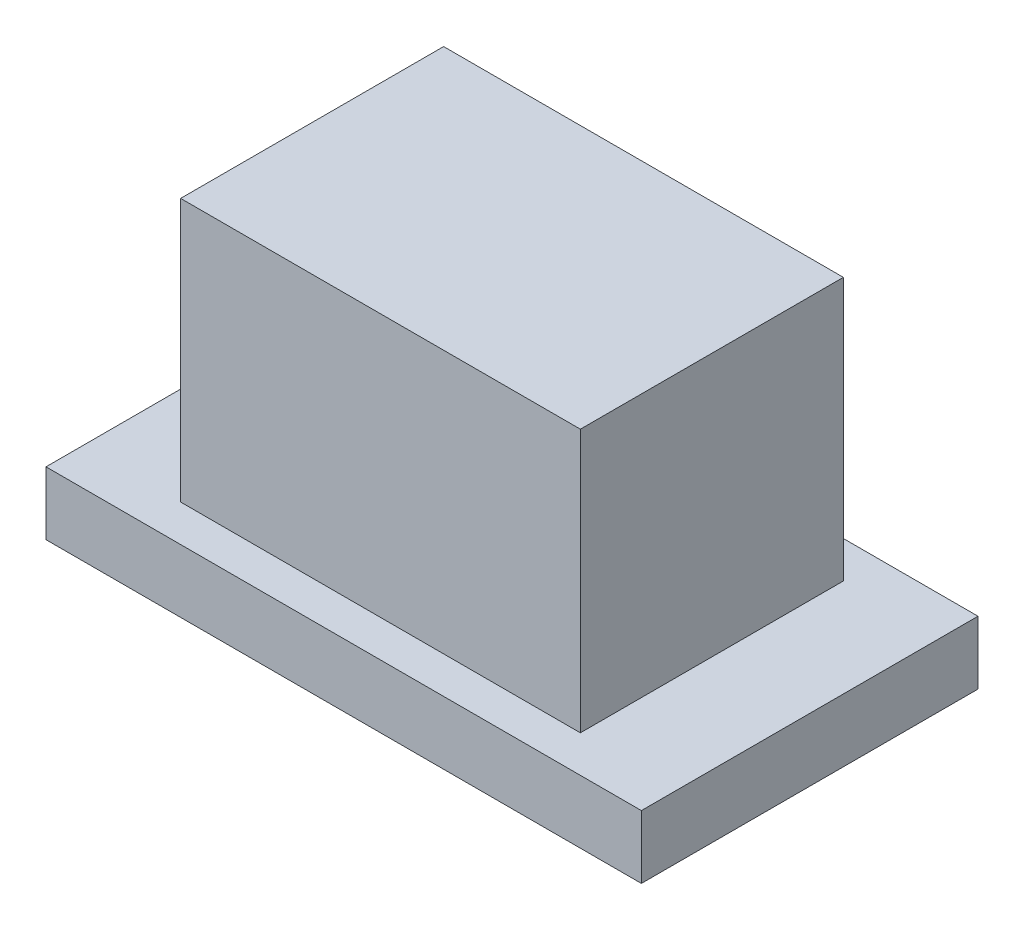
SolidWorks part; units mm, degrees
ref_plane "Front Plane" through (0, 0, 0) normal (0, 0, 1) x (1, 0, 0)
ref_plane "Top Plane" through (0, 0, 0) normal (0, 1, 0) x (1, 0, 0)
ref_plane "Right Plane" through (0, 0, 0) normal (1, 0, 0) x (0, 0, -1)
sketch "Sketch1" plane through (0, 0, 0) normal (0, 1, 0) x (1, 0, 0)
  line L1 (-8.6633, 6.0372) -> (19.6367, 6.0372)
  line L2 (-8.6633, 6.0372) -> (-8.6633, -9.9628)
  line L3 (-8.6633, -9.9628) -> (19.6367, -9.9628)
  line L4 (19.6367, 6.0372) -> (19.6367, -9.9628)
  point P4 (19.6367, -1.9628)
  dimension "D1" = 28.3
  dimension "D2" = 16
extrude "Boss-Extrude1" add sketch "Sketch1" along normal blind 3
sketch "Sketch2" plane through (0, 3, 0) normal (0, 1, 0) x (1, 0, 0)
  line L0 (5.4867, 6.0372) -> (5.4867, -9.9628) construction
  line L1 (-4.0133, 4.2872) -> (14.9867, 4.2872)
  line L2 (-4.0133, 4.2872) -> (-4.0133, -8.2128)
  line L3 (-4.0133, -8.2128) -> (14.9867, -8.2128)
  line L4 (14.9867, 4.2872) -> (14.9867, -8.2128)
  line L5 (19.6367, 6.0372) -> (-8.6633, 6.0372) construction
  line L6 (-8.6633, -9.9628) -> (19.6367, -9.9628) construction
  line L7 (-8.6633, -1.9628) -> (19.6367, -1.9628) construction
  line L8 (-8.6633, 6.0372) -> (-8.6633, -9.9628) construction
  line L9 (19.6367, -9.9628) -> (19.6367, 6.0372) construction
  point P16 (-4.0133, -1.9628)
  point P17 (5.4867, 4.2872)
  dimension "D1" = 19
  dimension "D2" = 12.5
extrude "Boss-Extrude2" add sketch "Sketch2" along normal blind 12.5
